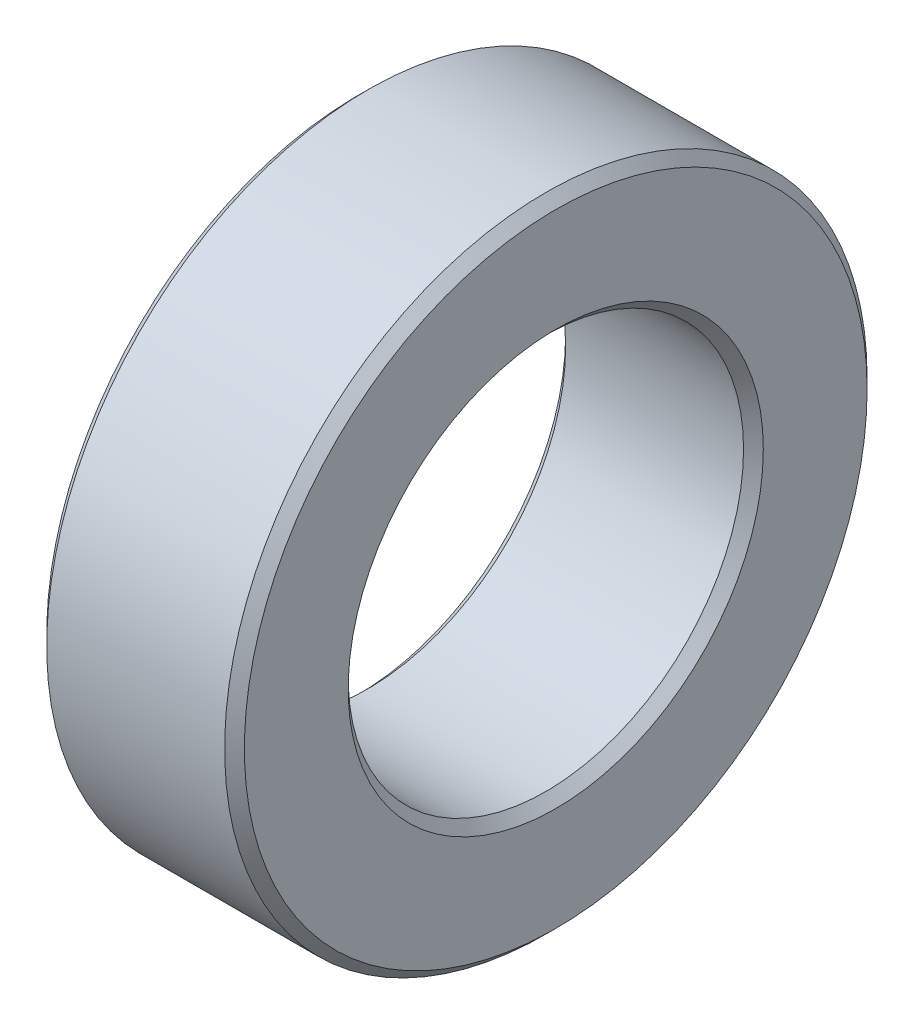
SolidWorks part; units mm, degrees
ref_plane "Front Plane" through (0, 0, 0) normal (0, 0, 1) x (1, 0, 0)
ref_plane "Top Plane" through (0, 0, 0) normal (0, 1, 0) x (1, 0, 0)
ref_plane "Right Plane" through (0, 0, 0) normal (1, 0, 0) x (0, 0, -1)
sketch "Sketch1" plane through (0, 0, 0) normal (1, 0, 0) x (0, 0, -1)
  circle A0 centre (0, 0) radius 6.5
  circle A1 centre (0, 0) radius 4
  dimension "D1" = 13
  dimension "D2" = 8
extrude "Boss-Extrude1" add sketch "Sketch1" along normal blind 4
chamfer "Chamfer1" distance 0.2 angle 45 4 edges at (0, 0, -4) (0, 0, -6.5) (4, 0, -4) (4, 0, -6.5)
